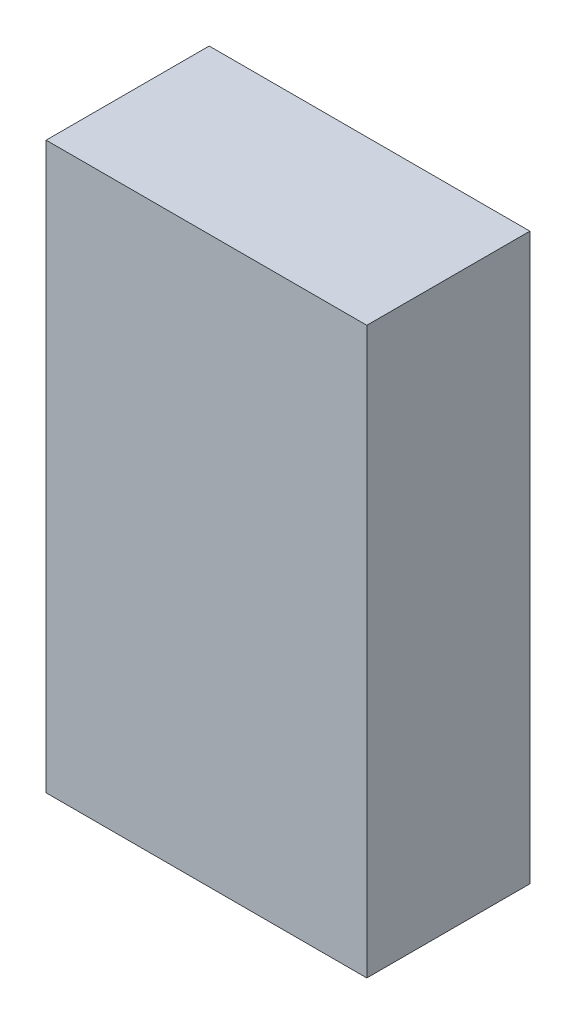
SolidWorks part; units mm, degrees
ref_plane "Front Plane" through (0, 0, 0) normal (0, 0, 1) x (1, 0, 0)
ref_plane "Top Plane" through (0, 0, 0) normal (0, 1, 0) x (1, 0, 0)
ref_plane "Right Plane" through (0, 0, 0) normal (1, 0, 0) x (0, 0, -1)
sketch "Sketch1" plane through (0, 0, 0) normal (0, 1, 0) x (1, 0, 0)
  line L1 (374.65, -190.5) -> (-374.65, -190.5)
  line L2 (374.65, -190.5) -> (374.65, 190.5)
  line L3 (374.65, 190.5) -> (-374.65, 190.5)
  line L4 (-374.65, -190.5) -> (-374.65, 190.5)
  line L5 (374.65, -190.5) -> (-374.65, 190.5) construction
  line L6 (374.65, 190.5) -> (-374.65, -190.5) construction
  point P0 (0, 0)
  dimension "D1" = 749.3
  dimension "D2" = 381
extrude "Boss-Extrude1" add sketch "Sketch1" along normal blind 1320.8
